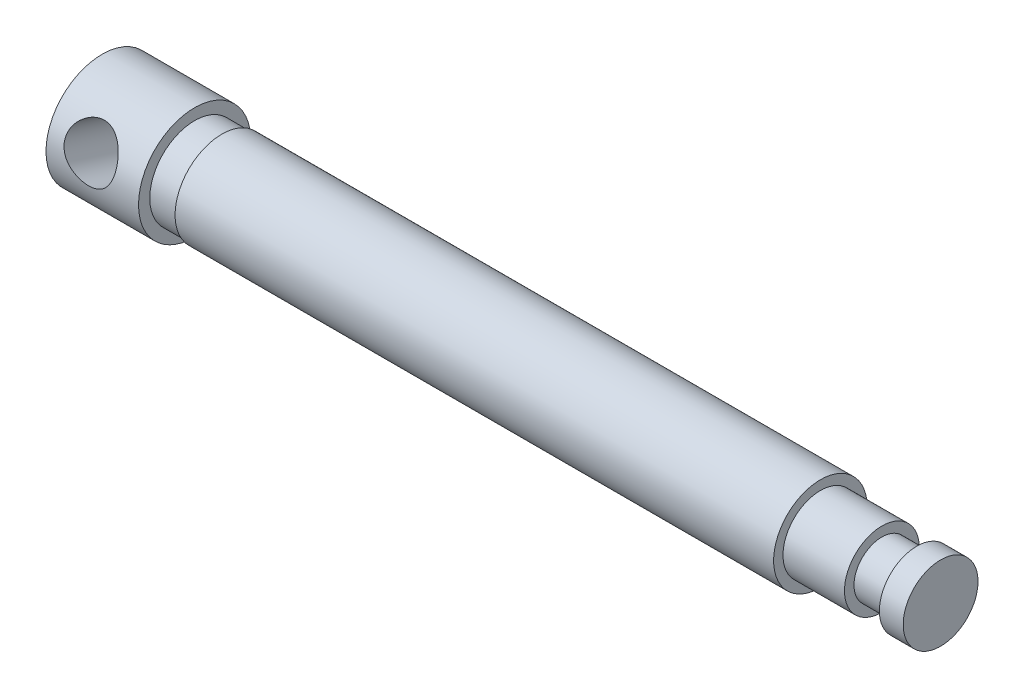
SolidWorks part; units mm, degrees
ref_plane "Front Plane" through (0, 0, 0) normal (0, 0, 1) x (1, 0, 0)
ref_plane "Top Plane" through (0, 0, 0) normal (0, 1, 0) x (1, 0, 0)
ref_plane "Right Plane" through (0, 0, 0) normal (1, 0, 0) x (0, 0, -1)
sketch "Sketch1" plane through (0, 0, 0) normal (0, 0, 1) x (1, 0, 0)
  line L0 (158.75, 0) -> (223.4152, 0) construction
  line L1 (0, 0) -> (20.32, 0)
  line L2 (20.32, 0) -> (20.32, -7.62)
  line L3 (20.32, -7.62) -> (15.7061, -7.62)
  line L4 (15.7061, -7.62) -> (15.7061, -9.525)
  line L5 (15.7061, -9.525) -> (0, -9.525)
  line L6 (0, -9.525) -> (0, 0)
  dimension "D1" = 9.525
  dimension "D2" = 20.32
  dimension "D3" = 7.62
  dimension "D4" = 15.7061
revolve "Revolve1" add sketch "Sketch1" angle 360 about L0
sketch "Sketch4" plane through (20.32, 0, 0) normal (1, 0, 0) x (0, 0, -1)
  circle A0 centre (0, 0) radius 7.9375
  dimension "D1" = 15.875
extrude "Extrude1" add sketch "Sketch4" along normal blind 101.6
cosmetic thread "Cosmetic Thread1"
sketch "Sketch5" plane through (0, 0, 0) normal (0, 0, 1) x (1, 0, 0)
  line L0 (121.92, 6.35) -> (132.3546, 6.35)
  line L1 (121.92, -7.9375) -> (121.92, 7.9375) construction
  line L2 (132.3546, 6.35) -> (132.3546, 4.7336)
  line L3 (132.3546, 4.7336) -> (138.2813, 4.7336)
  line L4 (138.2813, 4.7336) -> (138.2813, 6.35)
  line L5 (138.2813, 6.35) -> (142.3223, 6.35)
  line L6 (142.3223, 6.35) -> (142.3223, 0)
  line L7 (142.3223, 0) -> (121.92, 0)
  line L8 (121.92, 0) -> (121.92, 6.35)
  dimension "D1" = 20.4023
  dimension "D2" = 6.35
revolve "Revolve2" add sketch "Sketch5" angle 360 about L7
hole_wizard "11/32 (0.34375) Diameter Hole1" positions "3DSketch1" profile "Sketch3" hole size "11/32" standard "Ansi Inch"
sketch3d "3DSketch1"
  point P0 (10.3187, 0, 9.525)
  point P1 (7.1083, 2.913, 9.0686)
sketch "Sketch3" plane through (7.1083, 2.913, 9.0686) normal (1, 0, 0) x (0, -0.9521, 0.3058)
  line L0 (0, 0) -> (0, 21.5067)
  line L1 (0, 21.5067) -> (4.3663, 21.5067)
  line L2 (4.3663, 21.5067) -> (4.3663, 0)
  line L5 (4.3663, 0) -> (0, 0)
  line L11 (0, -6.35) -> (0, 107.95) construction
  dimension "Thru Hole Dia." = 8.7325
  dimension "Thru Hole Depth" = 21.5067
